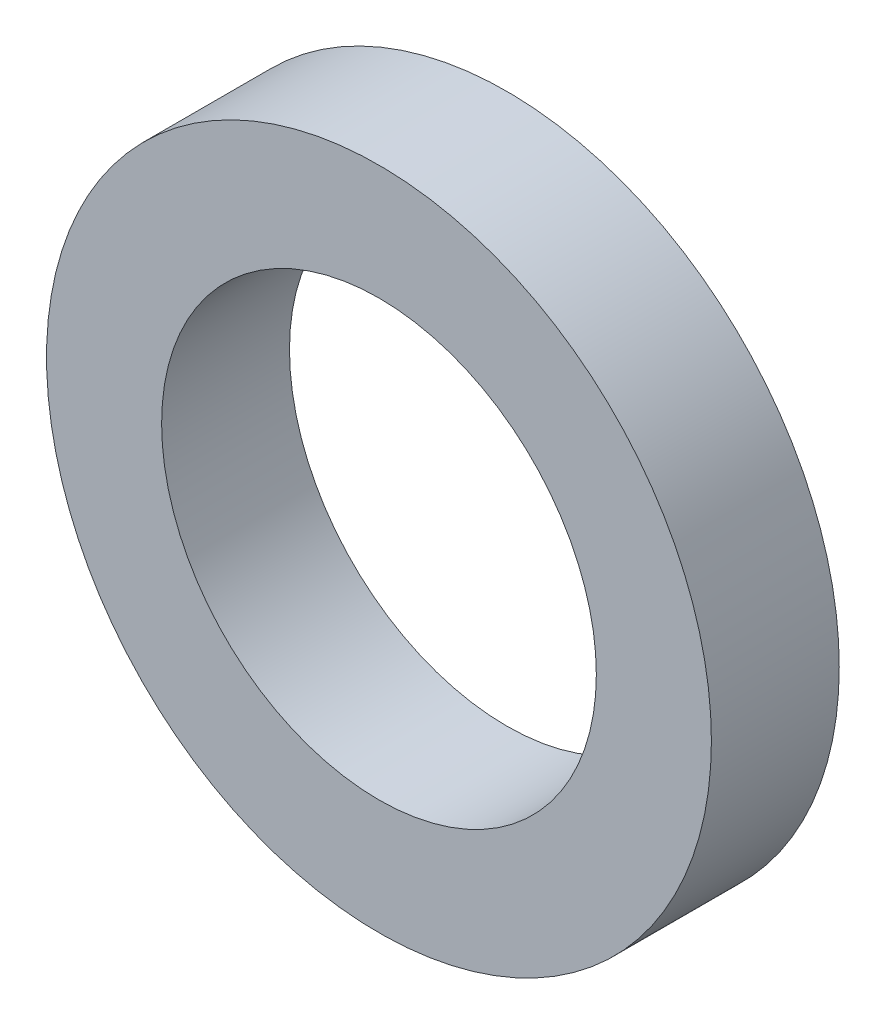
SolidWorks part; units mm, degrees
material "Литая легированная сталь"
ref_plane "Спереди" through (0, 0, 0) normal (0, 0, 1) x (1, 0, 0)
ref_plane "Сверху" through (0, 0, 0) normal (0, 1, 0) x (1, 0, 0)
ref_plane "Справа" through (0, 0, 0) normal (1, 0, 0) x (0, 0, -1)
sketch "Эскиз1" plane through (0, 0, 0) normal (0, 0, 1) x (1, 0, 0)
  circle A0 centre (0, 0) radius 8.5
  circle A1 centre (0, 0) radius 13
  dimension "D1" = 26
  dimension "D2" = 17
extrude "Бобышка-Вытянуть1" add sketch "Эскиз1" along normal blind 5
